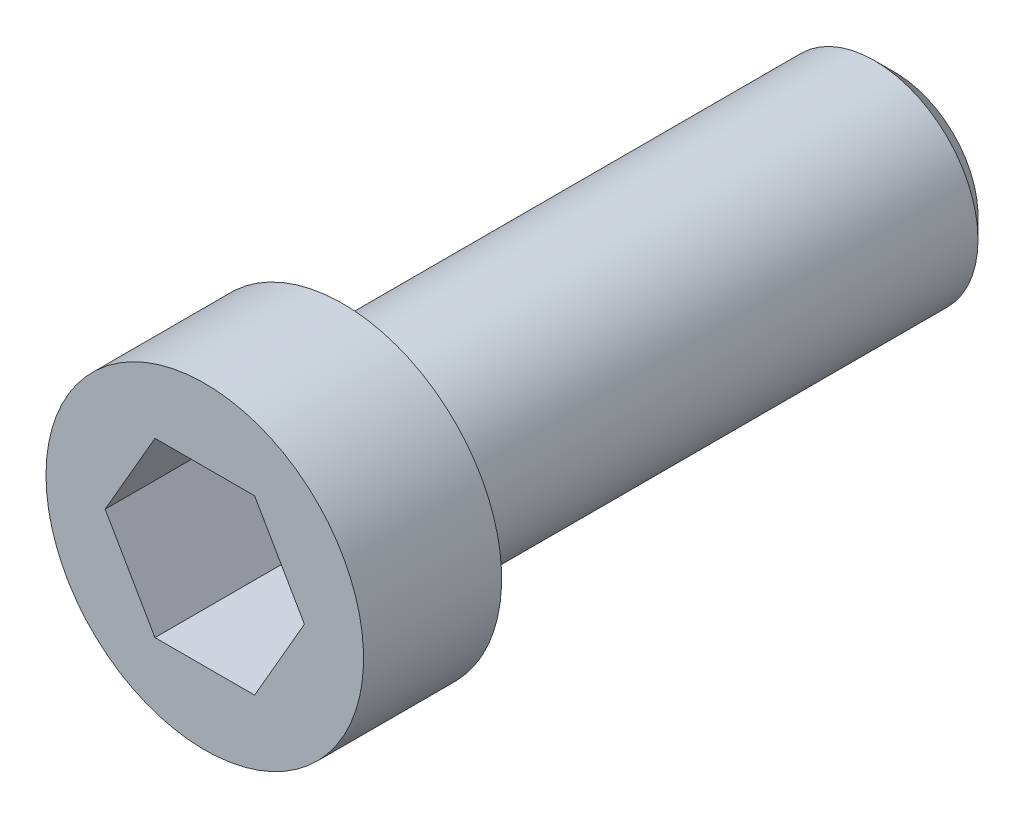
SolidWorks part; units mm, degrees
material "Простая углеродистая сталь"
ref_plane "Спереди" through (0, 0, 0) normal (0, 0, 1) x (1, 0, 0)
ref_plane "Сверху" through (0, 0, 0) normal (0, 1, 0) x (1, 0, 0)
ref_plane "Справа" through (0, 0, 0) normal (1, 0, 0) x (0, 0, -1)
sketch "Эскиз1" plane through (0, 0, 0) normal (1, 0, 0) x (0, 0, -1)
  line L0 (0, 0) -> (0, 2.3)
  line L1 (0, 2.3) -> (2, 2.3)
  line L2 (2, 2.3) -> (2, 1.5)
  line L3 (2, 1.5) -> (10, 1.5)
  line L4 (10, 1.5) -> (10, 0)
  line L5 (10, 0) -> (0, 0)
  line L6 (0, 0) -> (-1.7761, 0) construction
  dimension "D1" = 4.6
  dimension "D2" = 2
  dimension "D3" = 8
  dimension "D4" = 3
revolve "Повернуть1" add sketch "Эскиз1" angle 360 about L6
sketch "Эскиз2" plane through (0, 0, 0) normal (0, 0, 1) x (1, 0, 0)
  line L0 (0, 0) -> (0.8127, 0) construction
  line L1 (1.4434, 0) -> (0.7217, 1.25)
  line L2 (0.7217, 1.25) -> (-0.7217, 1.25)
  line L3 (-0.7217, 1.25) -> (-1.4434, 0)
  line L4 (-1.4434, 0) -> (-0.7217, -1.25)
  line L5 (-0.7217, -1.25) -> (0.7217, -1.25)
  line L6 (0.7217, -1.25) -> (1.4434, 0)
  circle A0 centre (0, 0) radius 1.25 construction
  dimension "D1" = 2.5
  dimension "D2" = 60
extrude "Вырез-Вытянуть1" cut sketch "Эскиз2" against normal blind 2
fillet "Скругление1" radius 0.3 1 edges at (-1.5, 0, -2)
chamfer "Фаска1" distance 0.3 angle 45 1 edges at (-1.5, 0, -10)
